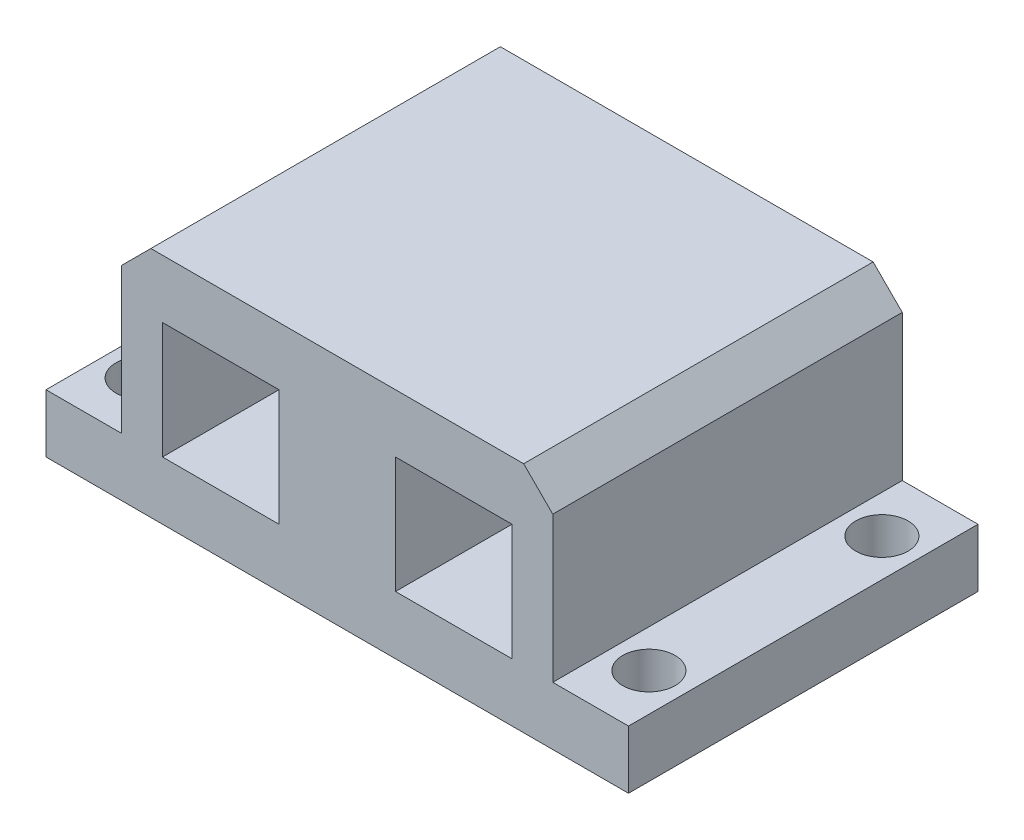
SolidWorks part; units mm, degrees
ref_plane "Front" through (0, 0, 0) normal (0, 0, 1) x (1, 0, 0)
ref_plane "Top" through (0, 0, 0) normal (0, 1, 0) x (1, 0, 0)
ref_plane "Right" through (0, 0, 0) normal (1, 0, 0) x (0, 0, -1)
sketch "Sketch2" plane through (0, 0, 0) normal (0, 0, 1) x (1, 0, 0)
  line L0 (-5, 5) -> (-5, -5)
  line L1 (-25, -10) -> (25, -10)
  line L2 (-25, -10) -> (-25, -5)
  line L3 (-18.5, 10) -> (18.5, 10)
  line L4 (25, -10) -> (25, -5)
  line L5 (-25, -10) -> (25, 10) construction
  line L6 (-25, 10) -> (25, -10) construction
  line L7 (-15, -5) -> (-5, -5)
  line L8 (-15, -5) -> (-15, 5)
  line L9 (-15, 5) -> (-5, 5)
  line L10 (15, -5) -> (15, 5)
  line L11 (-15, -5) -> (15, 5) construction
  line L12 (-15, 5) -> (15, -5) construction
  line L13 (5, 5) -> (5, -5)
  line L14 (5, 5) -> (15, 5)
  line L15 (5, -5) -> (15, -5)
  line L16 (-25, -5) -> (-18.5, -5)
  line L17 (-18.5, -5) -> (-18.5, 10)
  line L18 (18.5, 10) -> (18.5, -5)
  line L19 (18.5, -5) -> (25, -5)
  point P0 (0, 0)
  point P6 (0, 0)
  dimension "D1" = 20
  dimension "D2" = 50
  dimension "D3" = 10
  dimension "D4" = 10
  dimension "D5" = 10
  dimension "D6" = 10
  dimension "D7" = 5
  dimension "D8" = 10
  dimension "D9" = 3.5
  dimension "D10" = 3.5
extrude "Boss-Extrude1" add sketch "Sketch2" along normal blind 30
chamfer "Chamfer1" distance 2.5 angle 45 2 edges at (-18.5, 10, 15) (18.5, 10, 15)
sketch "Sketch3" plane through (0, -5, 0) normal (0, 1, 0) x (1, 0, 0)
  line L0 (0, 0) -> (0, -30) construction
  line L1 (16, -30) -> (-16, -30) construction
  line L2 (-18.5, 0) -> (-25, 0) construction
  line L3 (-18.5, -30) -> (-25, -30) construction
  circle A0 centre (-21.75, -5) radius 2.25
  circle A1 centre (-21.75, -25) radius 2.25
  circle A2 centre (21.75, -25) radius 2.25
  circle A3 centre (21.75, -5) radius 2.25
  dimension "D3" = 4.5
  dimension "D1" = 5
  dimension "D2" = 5
extrude "Cut-Extrude1" cut sketch "Sketch3" against normal through all contours A0 | A1 | A2 | A3
